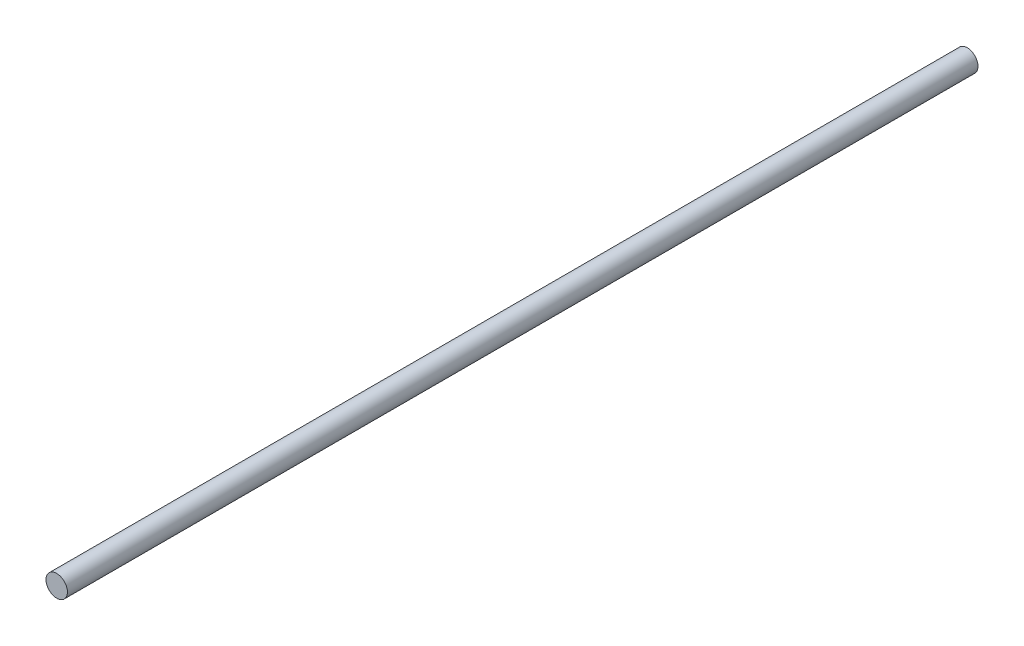
SolidWorks part; units mm, degrees
ref_plane "Front Plane" through (0, 0, 0) normal (0, 0, 1) x (1, 0, 0)
ref_plane "Top Plane" through (0, 0, 0) normal (0, 1, 0) x (1, 0, 0)
ref_plane "Right Plane" through (0, 0, 0) normal (1, 0, 0) x (0, 0, -1)
sketch "Sketch1" plane through (0, 0, 0) normal (0, 0, 1) x (1, 0, 0)
  circle A0 centre (0, 0) radius 2.0955
  dimension "D1" = 4.191
extrude "Extrude1" add sketch "Sketch1" along normal mid plane 177.8
